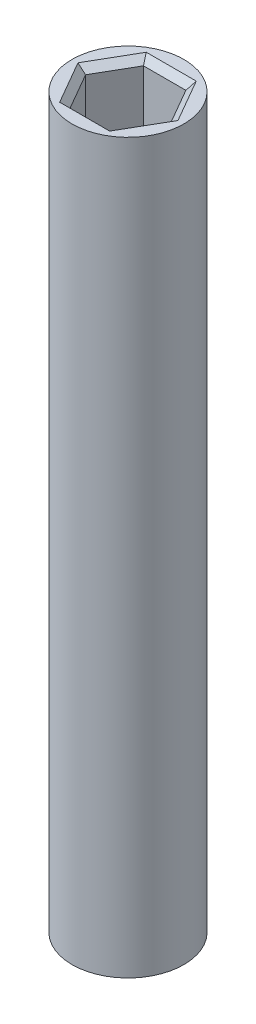
SolidWorks part; units mm, degrees
material "ABS"
ref_plane "Front Plane" through (0, 0, 0) normal (0, 0, 1) x (1, 0, 0)
ref_plane "Top Plane" through (0, 0, 0) normal (0, 1, 0) x (1, 0, 0)
ref_plane "Right Plane" through (0, 0, 0) normal (1, 0, 0) x (0, 0, -1)
sketch "Sketch1" plane through (0, 0, 0) normal (0, 1, 0) x (1, 0, 0)
  circle A0 centre (0, 0) radius 4.25
  dimension "D1" = 8.5
extrude "Boss-Extrude1" add sketch "Sketch1" along normal blind 55.3238
sketch "Sketch2" plane through (0, 55.3238, 0) normal (0, 1, 0) x (1, 0, 0)
  line L1 (1.6108, 2.79) -> (-1.6108, 2.79)
  line L2 (-1.6108, 2.79) -> (-3.2216, 0)
  line L3 (-3.2216, 0) -> (-1.6108, -2.79)
  line L4 (-1.6108, -2.79) -> (1.6108, -2.79)
  line L5 (1.6108, -2.79) -> (3.2216, 0)
  line L6 (3.2216, 0) -> (1.6108, 2.79)
  circle A0 centre (0, 0) radius 2.79 construction
  dimension "D1" = 5.58
extrude "Cut-Extrude1" cut sketch "Sketch2" against normal blind 6.6
chamfer "Chamfer1" distance 0.5 angle 45 6 edges at (0, 55.3238, 2.79) (2.4162, 55.3238, 1.395) (2.4162, 55.3238, -1.395) (0, 55.3238, -2.79) (-2.4162, 55.3238, 1.395) (-2.4162, 55.3238, -1.395)
sketch "Sketch3" plane through (0, 0, 0) normal (0, -1, 0) x (1, 0, 0)
  line L1 (0, 3.2216) -> (-2.79, 1.6108)
  line L2 (-2.79, 1.6108) -> (-2.79, -1.6108)
  line L3 (-2.79, -1.6108) -> (0, -3.2216)
  line L4 (0, -3.2216) -> (2.79, -1.6108)
  line L5 (2.79, -1.6108) -> (2.79, 1.6108)
  line L6 (2.79, 1.6108) -> (0, 3.2216)
  circle A0 centre (0, 0) radius 2.79 construction
  dimension "D1" = 5.58
extrude "Cut-Extrude2" cut sketch "Sketch3" against normal blind 6.6
chamfer "Chamfer2" distance 0.5 angle 45 6 edges at (1.395, 0, 2.4162) (-1.395, 0, 2.4162) (-2.79, 0, 0) (-1.395, 0, -2.4162) (1.395, 0, -2.4162) (2.79, 0, 0)
sketch3d "3DSketch1"
  line L0 (0, 0, 0) -> (0, 55.3238, 0)
